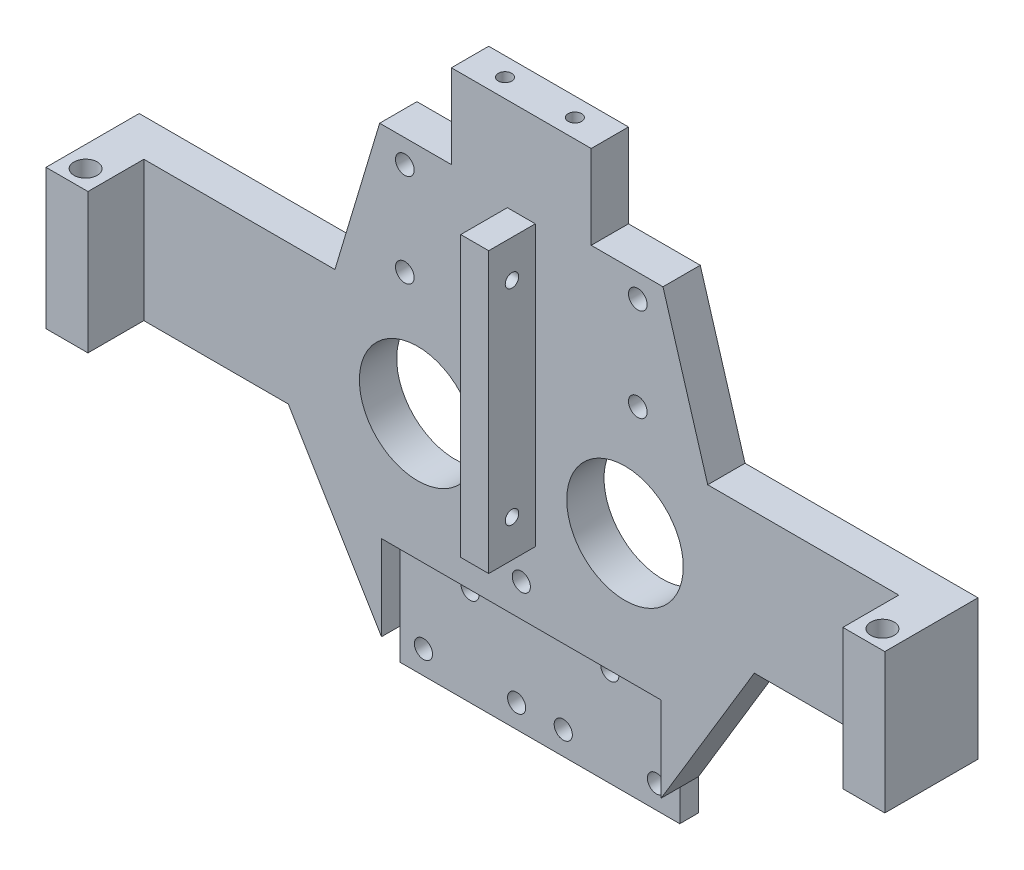
SolidWorks part; units mm, degrees
material "PLA Black"
ref_plane "Front Plane" through (0, 0, 0) normal (0, 0, 1) x (1, 0, 0)
ref_plane "Top Plane" through (0, 0, 0) normal (0, 1, 0) x (1, 0, 0)
ref_plane "Right Plane" through (0, 0, 0) normal (1, 0, 0) x (0, 0, -1)
sketch "Sketch1" plane through (0, 0, 0) normal (0, 0, 1) x (1, 0, 0)
  line L0 (-40, -10) -> (-25, 40)
  line L1 (-90, -10) -> (-40, -10)
  line L2 (-90, -10) -> (-90, -40)
  line L4 (0, 40) -> (0, -40) construction
  line L5 (-25, 40) -> (25, 40)
  line L6 (25, 40) -> (40, -10)
  line L7 (-90, -40) -> (90, -40)
  line L8 (40, -10) -> (90, -10)
  line L11 (90, -10) -> (90, -40)
  point P2 (0, 0)
  dimension "D1" = 30
  dimension "D2" = 50
  dimension "D3" = 80
  dimension "D4" = 180
  dimension "D5" = 50
extrude "Extrude1" add sketch "Sketch1" along normal blind 8
sketch "Sketch2" plane through (0, 0, 0) normal (0, 0, 1) x (1, 0, 0)
  line L0 (-90, -40) -> (90, -40) construction
  line L1 (-50, -40) -> (50, -40)
  line L2 (-50, -40) -> (-50, -80) construction
  line L3 (-50, -80) -> (50, -80) construction
  line L4 (50, -40) -> (50, -80) construction
  line L5 (30, -80) -> (30, -73.2445)
  line L6 (30, -73.2445) -> (50, -40)
  line L7 (30, -80) -> (-30, -80)
  line L8 (-30, -80) -> (-30, -73.2445)
  line L9 (-30, -73.2445) -> (-50, -40)
  point P6 (0, -80)
  dimension "D1" = 100
  dimension "D2" = 40
  dimension "D3" = 60
extrude "Extrude2" add sketch "Sketch2" along normal up to surface (8 mm away) up to face at (0, -5, 8)
sketch "Sketch4" plane through (0, 0, 8) normal (0, 0, 1) x (1, 0, 0)
  line L0 (0, 40) -> (0, -80) construction
  line L1 (-3, 20) -> (3, 20)
  line L2 (-3, 20) -> (-3, -40)
  line L3 (-3, -40) -> (3, -40)
  line L4 (3, 20) -> (3, -40)
  line L5 (25, 40) -> (-25, 40) construction
  point P10 (0, 20)
  dimension "D1" = 6
  dimension "D2" = 60
  dimension "D3" = 20
extrude "Extrude3" add sketch "Sketch4" along normal blind 10
hole_wizard "Ø4.0 (4) Diameter Hole2" positions "3DSketch2" profile "Sketch5" hole size "Ø4.0" standard "Ansi Metric"
sketch3d "3DSketch2"
  line L0 (0, 40, 0) -> (0, -80, 0) construction
  line L1 (25, 40, 0) -> (-25, 40, 0) construction
  point P0 (25, -3, 0)
  point P2 (-25, -3, 0)
  point P16 (25, 17, 0)
  point P18 (-25, 17, 0)
  dimension "D1" = 25
  dimension "D2" = 25
  dimension "D3" = 23
  dimension "D4" = 20
sketch "Sketch5" plane through (25, -3, 0) normal (1, 0, 0) x (0, 1, 0)
  line L0 (0, 0) -> (0, 15)
  line L1 (0, 15) -> (2, 15)
  line L2 (2, 15) -> (2, 0)
  line L5 (2, 0) -> (0, 0)
  line L10 (0, 15) -> (-2, 15) construction
  line L11 (0, -6.35) -> (0, 107.95) construction
  dimension "Hole Dia." = 4
  dimension "Hole Depth" = 15
  dimension "Drill Angle" = 180
sketch "Sketch6" plane through (0, 0, 8) normal (0, 0, 1) x (1, 0, 0)
  line L0 (-90, -40) -> (-50, -40) construction
  line L1 (-90, -10) -> (-81, -10)
  line L2 (-90, -10) -> (-90, -40)
  line L3 (-90, -40) -> (-81, -40)
  line L4 (-81, -10) -> (-81, -40)
  dimension "D1" = 9
extrude "Extrude4" add sketch "Sketch6" along normal blind 12
hole_wizard "Ø5.0 (5) Diameter Hole1" positions "3DSketch3" profile "Sketch8" hole size "Ø5.0" standard "Ansi Metric" end condition through all
sketch3d "3DSketch3"
  line L0 (-81, -10, 20) -> (-90, -10, 20) construction
  point P0 (-85.5, -10, 16)
  point P5 (-85.5, -10, 20)
  dimension "D1" = 4
sketch "Sketch8" plane through (-85.5, -10, 16) normal (1, 0, 0) x (0, 0, 1)
  line L0 (0, 0) -> (0, 70)
  line L1 (0, 70) -> (2.5, 70)
  line L2 (2.5, 70) -> (2.5, 0)
  line L5 (2.5, 0) -> (0, 0)
  line L11 (0, -6.35) -> (0, 107.95) construction
  dimension "Thru Hole Dia." = 5
  dimension "Thru Hole Depth" = 70
mirror "Mirror1" about plane through (0, 0, 0) normal (1, 0, 0) of "Ø5.0 (5) Diameter Hole1", "Extrude4"
hole_wizard "Ø2.9 (2.9) Diameter Hole1" positions "3DSketch4" profile "Sketch9" hole size "Ø2.9" standard "Ansi Metric"
sketch3d "3DSketch4"
  line L7 (-7.5, 40, 4) -> (7.5, 40, 4) construction
  line L9 (0, 40, 0) -> (0, 40, 8) construction
  line L10 (25, 40, 0) -> (-25, 40, 0) construction
  line L11 (25, 40, 8) -> (-25, 40, 8) construction
  point P0 (-7.5, 40, 4)
  point P2 (7.5, 40, 4)
  point P31 (0, 40, 4)
  point P32 (0, 40, 4)
  dimension "D1" = 15
sketch "Sketch9" plane through (-7.5, 40, 4) normal (1, 0, 0) x (0, 0, 1)
  line L0 (0, 0) -> (0, 10)
  line L1 (0, 10) -> (1.45, 10)
  line L2 (1.45, 10) -> (1.45, 0)
  line L5 (1.45, 0) -> (0, 0)
  line L10 (0, 10) -> (-1.45, 10) construction
  line L11 (0, -6.35) -> (0, 107.95) construction
  dimension "Hole Dia." = 2.9
  dimension "Hole Depth" = 10
  dimension "Drill Angle" = 180
sketch "Sketch10" plane through (0, 0, 8) normal (0, 0, 1) x (1, 0, 0)
  circle A0 centre (-22.2487, -27.8884) radius 12.5
  dimension "D1" = 25
extrude "Extrude5" cut sketch "Sketch10" against normal blind 10
mirror "Mirror2" about plane through (0, 0, 0) normal (1, 0, 0) of "Extrude5"
hole_wizard "Ø2.9 (2.9) Diameter Hole2" positions "3DSketch5" profile "Sketch11" hole size "Ø2.9" standard "Ansi Metric"
sketch3d "3DSketch5"
  line L0 (-3, 20, 13) -> (-3, -40, 13) construction
  line L1 (-3, 20, 18) -> (-3, 20, 8) construction
  line L2 (-3, -40, 18) -> (-3, -40, 8) construction
  point P0 (-3, 12, 13)
  point P2 (-3, -32, 13)
  dimension "D1" = 44
  dimension "D2" = 8
sketch "Sketch11" plane through (-3, 12, 13) normal (0, 1, 0) x (0, 0, 1)
  line L0 (0, 0) -> (0, 10)
  line L1 (0, 10) -> (1.45, 10)
  line L2 (1.45, 10) -> (1.45, 0)
  line L5 (1.45, 0) -> (0, 0)
  line L10 (0, 10) -> (-1.45, 10) construction
  line L11 (0, -6.35) -> (0, 107.95) construction
  dimension "Hole Dia." = 2.9
  dimension "Hole Depth" = 10
  dimension "Drill Angle" = 180
sketch "Sketch14" plane through (0, 0, 0) normal (0, 0, -1) x (-1, 0, 0)
  line L0 (-30.4, 22) -> (-15, 22)
  line L1 (-40, -10) -> (-25, 40) construction
  line L2 (-15, 22) -> (-15, 40)
  line L3 (-25, 40) -> (25, 40) construction
  line L4 (-15, 40) -> (-25, 40)
  line L5 (-25, 40) -> (-30.4, 22)
  line L6 (25, 40) -> (15, 40)
  line L7 (15, 40) -> (15, 22)
  line L8 (15, 22) -> (30.4, 22)
  line L9 (25, 40) -> (40, -10) construction
  line L10 (30.4, 22) -> (25, 40)
  dimension "D1" = 30
  dimension "D2" = 18
extrude "Extrude8" cut sketch "Sketch14" against normal through all
sketch "Sketch15" plane through (0, 0, 8) normal (0, 0, 1) x (1, 0, 0)
  line L0 (30, -80) -> (30, -73.2445) construction
  line L1 (-30, -80) -> (30, -80)
  line L2 (-30, -80) -> (-30, -55)
  line L3 (-30, -55) -> (30, -55)
  line L4 (30, -80) -> (30, -55)
  dimension "D1" = 25
extrude "Extrude9" cut sketch "Sketch15" against normal blind 4
hole_wizard "Ø4.0 (4) Diameter Hole4" positions "3DSketch7" profile "Sketch16" hole size "Ø4.0" standard "Ansi Metric"
sketch3d "3DSketch7"
  line L0 (-15, -59, 4) -> (15, -59, 4) construction
  line L4 (-25, -75, 4) -> (25, -75, 4) construction
  line L6 (0, -55, 4) -> (0, -80, 4) construction
  line L7 (30, -55, 4) -> (-30, -55, 4) construction
  line L8 (-30, -80, 4) -> (30, -80, 4) construction
  line L11 (15, -55, 4) -> (15, -80, 4) construction
  line L13 (30, -73.2445, 4) -> (30, -55, 4) construction
  line L14 (30, -80, 4) -> (30, -73.2445, 4) construction
  line L15 (-30, -73.2445, 4) -> (-30, -80, 4) construction
  point P0 (15, -59, 4)
  point P2 (5, -75, 4)
  point P4 (25, -75, 4)
  point P6 (-5, -75, 4)
  point P8 (-25, -75, 4)
  point P10 (-15, -59, 4)
  point P36 (0, -59, 4)
  point P37 (0, -75, 4)
  dimension "D1" = 15
  dimension "D2" = 20
  dimension "D3" = 16
  dimension "D4" = 5
  dimension "D5" = 20
  dimension "D6" = 5
  dimension "D7" = 4
sketch "Sketch16" plane through (15, -59, 4) normal (1, 0, 0) x (0, -1, 0)
  line L0 (0, 0) -> (0, 15)
  line L1 (0, 15) -> (1.95, 15)
  line L2 (1.95, 15) -> (1.95, 0)
  line L5 (1.95, 0) -> (0, 0)
  line L10 (0, 15) -> (-1.95, 15) construction
  line L11 (0, -6.35) -> (0, 107.95) construction
  dimension "Hole Dia." = 3.9
  dimension "Hole Depth" = 15
  dimension "Drill Angle" = 180
hole_wizard "Ø4.0 (4) Diameter Hole5" positions "3DSketch8" profile "Sketch17" hole size "Ø4.0" standard "Ansi Metric"
sketch3d "3DSketch8"
  line L0 (30, -55, 8) -> (-30, -55, 8) construction
  line L1 (-3, -40, 8) -> (3, -40, 8) construction
  point P0 (0, -48, 8)
  point P7 (0, -40, 8)
  dimension "D1" = 7
sketch "Sketch17" plane through (0, -48, 8) normal (1, 0, 0) x (0, -1, 0)
  line L0 (0, 0) -> (0, 15)
  line L1 (0, 15) -> (1.95, 15)
  line L2 (1.95, 15) -> (1.95, 0)
  line L5 (1.95, 0) -> (0, 0)
  line L10 (0, 15) -> (-1.95, 15) construction
  line L11 (0, -6.35) -> (0, 107.95) construction
  dimension "Hole Dia." = 3.9
  dimension "Hole Depth" = 15
  dimension "Drill Angle" = 180
